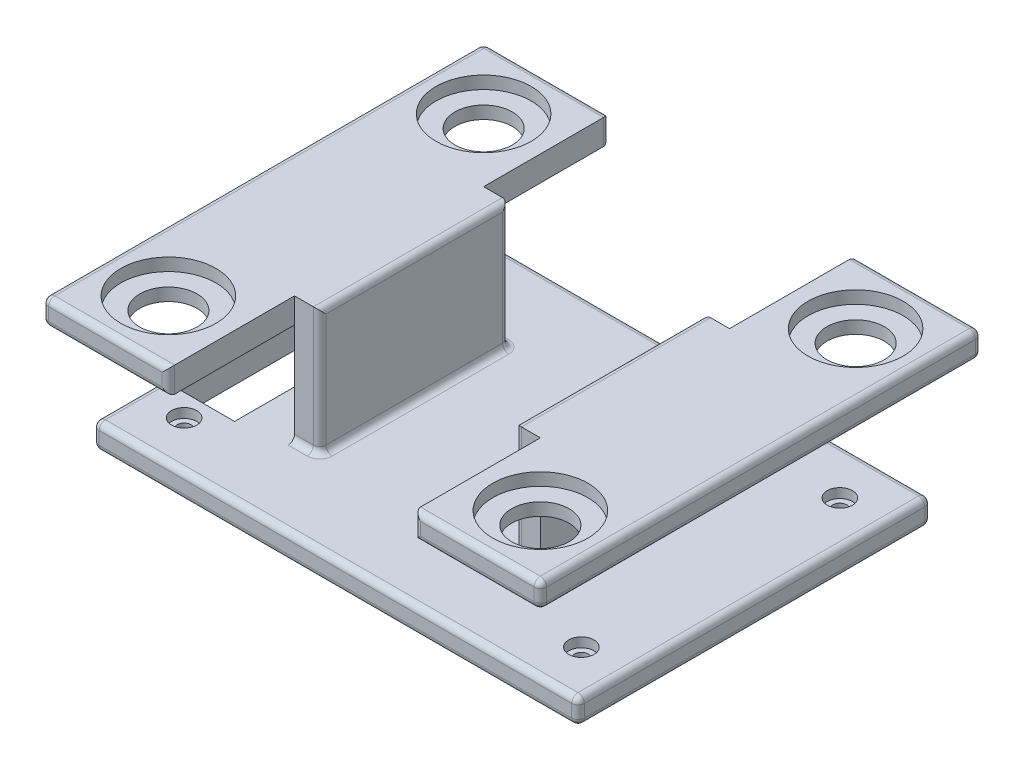
SolidWorks part; units mm, degrees
ref_plane "Front Plane" through (0, 0, 0) normal (0, 0, 1) x (1, 0, 0)
ref_plane "Top Plane" through (0, 0, 0) normal (0, 1, 0) x (1, 0, 0)
ref_plane "Right Plane" through (0, 0, 0) normal (1, 0, 0) x (0, 0, -1)
sketch "Sketch1" plane through (0, 0, 0) normal (0, 1, 0) x (1, 0, 0)
  line L1 (-31.5, 20.5) -> (31.5, 20.5) construction
  line L2 (-31.5, 20.5) -> (-31.5, -20.5) construction
  line L3 (-31.5, -20.5) -> (31.5, -20.5) construction
  line L4 (31.5, 20.5) -> (31.5, -20.5) construction
  line L5 (-31.5, 20.5) -> (31.5, -20.5) construction
  line L6 (-31.5, -20.5) -> (31.5, 20.5) construction
  line L7 (-38.4735, 28) -> (38.4735, 28)
  line L8 (-38.4735, 28) -> (-38.4735, -28)
  line L9 (-38.4735, -28) -> (38.4735, -28)
  line L10 (38.4735, 28) -> (38.4735, -28)
  line L11 (-38.4735, 28) -> (38.4735, -28) construction
  line L12 (-38.4735, -28) -> (38.4735, 28) construction
  line L13 (-36, 17) -> (-27, 17)
  line L14 (-36, 17) -> (-36, -17)
  line L15 (-36, -17) -> (-27, -17)
  line L16 (-27, 17) -> (-27, -17)
  line L17 (-36, 17) -> (-27, -17) construction
  line L18 (-36, -17) -> (-27, 17) construction
  line L20 (-31.5, 20.5) -> (-31.5, -20.5) construction
  line L24 (31.5, 20.5) -> (31.5, -20.5) construction
  circle A0 centre (-31.5, 20.5) radius 1.1
  circle A1 centre (-31.5, -20.5) radius 1.1
  circle A2 centre (31.5, -20.5) radius 1.1
  circle A3 centre (31.5, 20.5) radius 1.1
  point P0 (0, 0)
  point P6 (0, 0)
  point P15 (-31.5, 0)
  dimension "D5" = 2.2
  dimension "D1" = 63
  dimension "D2" = 41
  dimension "D3" = 6.9735
  dimension "D4" = 7.5
  dimension "D6" = 34
  dimension "D7" = 9
extrude "Boss-Extrude1" add sketch "Sketch1" along normal blind 4
sketch "Sketch6" plane through (0, 4, 0) normal (0, 1, 0) x (1, 0, 0)
  line L1 (-17.5, 15) -> (17.5, 15) construction
  line L2 (-17.5, 15) -> (-17.5, -15) construction
  line L3 (-17.5, -15) -> (17.5, -15) construction
  line L4 (17.5, 15) -> (17.5, -15) construction
  line L5 (-17.5, 15) -> (17.5, -15) construction
  line L6 (-17.5, -15) -> (17.5, 15) construction
  line L7 (-19.5, 15) -> (-15.5, 15)
  line L8 (-19.5, 15) -> (-19.5, -15)
  line L9 (-19.5, -15) -> (-15.5, -15)
  line L10 (-15.5, 15) -> (-15.5, -15)
  line L11 (-19.5, 15) -> (-15.5, -15) construction
  line L12 (-19.5, -15) -> (-15.5, 15) construction
  point P0 (0, 0)
  point P6 (-17.5, 0)
  dimension "D1" = 35
  dimension "D2" = 30
  dimension "D3" = 4
extrude "Boss-Extrude5" add sketch "Sketch6" along normal blind 20
sketch "Sketch7" plane through (-19.5, 0, 0) normal (-1, 0, 0) x (0, 0, 1)
  line L0 (15, 24) -> (15, 4) construction
  line L1 (-15, 24) -> (15, 24) construction
  line L3 (-15, 22) -> (15, 22) construction
  line L4 (-35, 24) -> (35, 24)
  line L5 (-35, 24) -> (-35, 20)
  line L6 (-35, 20) -> (35, 20)
  line L7 (35, 24) -> (35, 20)
  line L8 (-35, 24) -> (35, 20) construction
  line L9 (-35, 20) -> (35, 24) construction
  point P7 (0, 22)
  dimension "D1" = 2
  dimension "D2" = 4
  dimension "D3" = 70
extrude "Boss-Extrude6" add sketch "Sketch7" along normal blind 20
sketch "Sketch8" plane through (0, 24, 0) normal (0, 1, 0) x (1, 0, 0)
  line L0 (-29.5, 15) -> (-29.5, 25) construction
  line L1 (-39.5, -35) -> (-39.5, 35) construction
  line L2 (-19.5, 15) -> (-39.5, 15) construction
  line L3 (-19.5, 15) -> (-19.5, -15) construction
  line L4 (-19.5, -15) -> (-39.5, -15) construction
  line L5 (-29.5, 35) -> (-29.5, 25) construction
  line L6 (-39.5, 15) -> (-39.5, -15) construction
  line L7 (-39.5, 35) -> (-19.5, 35) construction
  line L8 (-29.5, -35) -> (-29.5, -25) construction
  line L9 (-39.5, -35) -> (-19.5, -35) construction
  circle A0 centre (-29.5, 25) radius 4.55
  circle A1 centre (-29.5, -25) radius 4.55
  dimension "D2" = 9.1
  dimension "D1" = 10
  dimension "D3" = 30
extrude "Cut-Extrude2" cut sketch "Sketch8" against normal up to surface (4 mm away) up to face at (-26.1667, 20, 0)
sketch "Sketch9" plane through (0, 24, 0) normal (0, 1, 0) x (1, 0, 0)
  circle A0 centre (-29.5, 25) radius 7.55
  circle A1 centre (-29.5, -25) radius 7.55
  circle A2 centre (-29.5, 25) radius 4.55 construction
  dimension "D1" = 3
extrude "Cut-Extrude3" cut sketch "Sketch9" against normal blind 2
mirror "Mirror2" about plane through (0, 0, 0) normal (1, 0, 0) of "Cut-Extrude3", "Cut-Extrude2", "Boss-Extrude6", "Boss-Extrude5"
sketch "Sketch10" plane through (0, 4, 0) normal (0, 1, 0) x (1, 0, 0)
  circle A0 centre (-31.5, -20.5) radius 2
  circle A1 centre (-31.5, 20.5) radius 2
  circle A2 centre (31.5, 20.5) radius 2
  circle A3 centre (31.5, -20.5) radius 2
  dimension "D1" = 4
extrude "Cut-Extrude4" cut sketch "Sketch10" against normal blind 1.5
fillet "Fillet4" radius 1 44 edges at (29.5, 20, -35) (29.5, 24, -35) (19.5, 22, -35) (-29.5, 24, -35) (-29.5, 20, -35) (-19.5, 22, -35) (-39.5, 20, 0) (-39.5, 22, -35) (-39.5, 24, 0) (-29.5, 20, 35) (-39.5, 22, 35) (-29.5, 24, 35) (-19.5, 22, 35) (29.5, 24, 35) (29.5, 20, 35) (19.5, 22, 35) (39.5, 24, 0) (39.5, 22, -35) (39.5, 20, 0) (39.5, 22, 35) (38.4735, 4, 0) (38.4735, 0, 0) (38.4735, 2, -28) (0, 4, -28) (0, 0, -28) (-38.4735, 2, -28) (-38.4735, 4, 0) (-38.4735, 0, 0) (-38.4735, 2, 28) (0, 4, 28) (38.4735, 2, 28) (0, 0, 28) (17.5, 4, -15) (17.5, 4, 15) (15.5, 14, -15) (15.5, 24, 0) (15.5, 14, 15) (15.5, 4, 0) (-17.5, 4, 15) (-17.5, 4, -15) (-15.5, 14, 15) (-15.5, 24, 0) (-15.5, 14, -15) (-15.5, 4, 0)
